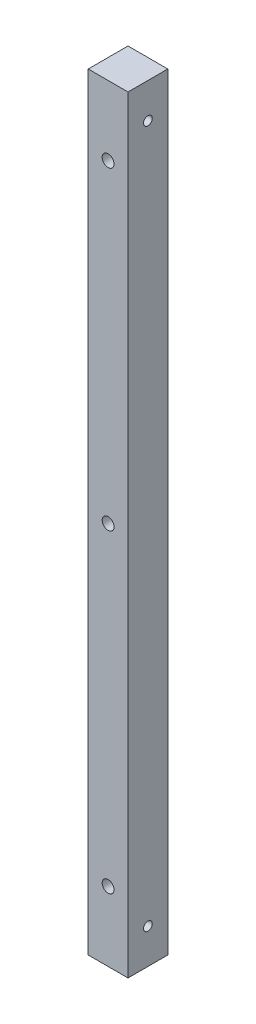
SolidWorks part; units mm, degrees
ref_plane "Plan de face" through (0, 0, 0) normal (0, 0, 1) x (1, 0, 0)
ref_plane "Plan de dessus" through (0, 0, 0) normal (0, 1, 0) x (1, 0, 0)
ref_plane "Plan de droite" through (0, 0, 0) normal (1, 0, 0) x (0, 0, -1)
sketch "Esquisse1" plane through (0, 0, 0) normal (0, 1, 0) x (1, 0, 0)
  line L1 (-5.7, 5.7) -> (5.7, 5.7)
  line L2 (-5.7, 5.7) -> (-5.7, -5.7)
  line L3 (-5.7, -5.7) -> (5.7, -5.7)
  line L4 (5.7, 5.7) -> (5.7, -5.7)
  line L5 (-5.7, 5.7) -> (5.7, -5.7) construction
  line L6 (-5.7, -5.7) -> (5.7, 5.7) construction
  point P0 (0, 0)
  dimension "D1" = 11.4
  dimension "D2" = 11.4
extrude "Boss.-Extru.1" add sketch "Esquisse1" along normal blind 219.772
sketch "Esquisse2" plane through (0, 0, 5.7) normal (0, 0, 1) x (1, 0, 0)
  line L0 (5.7, 219.772) -> (5.7, 0) construction
  line L1 (-5.7, 0) -> (5.7, 0) construction
  point P0 (0, 199.885)
  point P1 (0, 109.885)
  point P2 (0, 19.885)
  dimension "D1" = 5.7
  dimension "D2" = 5.7
  dimension "D3" = 5.7
  dimension "D4" = 90
  dimension "D5" = 90
  dimension "D6" = 109.885
hole_wizard "Dégagement M31" positions "Esquisse4" profile "Esquisse3" hole size "M3" standard "ISO" end condition through all
sketch "Esquisse4" plane through (0, 0, 5.7) normal (0, 0, 1) x (1, 0, 0)
  point P1 (0, 199.885)
  point P4 (0, 109.885)
  point P7 (0, 19.885)
sketch "Esquisse3" plane through (0, 199.885, 5.7) normal (1, 0, 0) x (0, -1, 0)
  line L0 (0, 0) -> (0, 11.4)
  line L1 (0, 11.4) -> (1.7, 11.4)
  line L2 (1.7, 11.4) -> (1.7, 0)
  line L5 (1.7, 0) -> (0, 0)
  line L11 (0, -6.35) -> (0, 107.95) construction
  dimension "Diamètre du perçage jusqu'au prochain" = 3.4
  dimension "Profondeur du perçage jusqu'au prochain" = 11.4
sketch "Esquisse5" plane through (5.7, 0, 0) normal (1, 0, 0) x (0, 0, -1)
  line L0 (-5.7, 219.772) -> (-5.7, 0) construction
  line L1 (-5.7, 219.772) -> (5.7, 219.772) construction
  point P0 (0, 209.772)
  point P1 (0, 10)
  dimension "D1" = 10
  dimension "D2" = 5.7
  dimension "D3" = 5.7
  dimension "D4" = 10
hole_wizard "Trou taraudé M31" positions "Esquisse7" profile "Esquisse6" tap size "M3" standard "ISO" end condition through all
sketch "Esquisse7" plane through (5.7, 0, 0) normal (1, 0, 0) x (0, 0, -1)
  point P1 (0, 209.772)
  point P4 (0, 10)
cosmetic thread "Filetage de perçage1" parameters "D2"=3
cosmetic thread "Filetage de perçage2" parameters "D2"=3
sketch "Esquisse6" plane through (5.7, 209.772, 0) normal (0, 1, 0) x (0, 0, -1)
  line L0 (0, 0) -> (0, 11.4)
  line L1 (0, 11.4) -> (1.25, 11.4)
  line L2 (1.25, 11.4) -> (1.25, 0)
  line L5 (1.25, 0) -> (0, 0)
  line L11 (0, -6.35) -> (0, 107.95) construction
  dimension "Diamètre du trou pour taraudage jusqu'au prochain" = 2.5
  dimension "Profondeur du trou pour taraudage jusqu'au prochain" = 11.4
